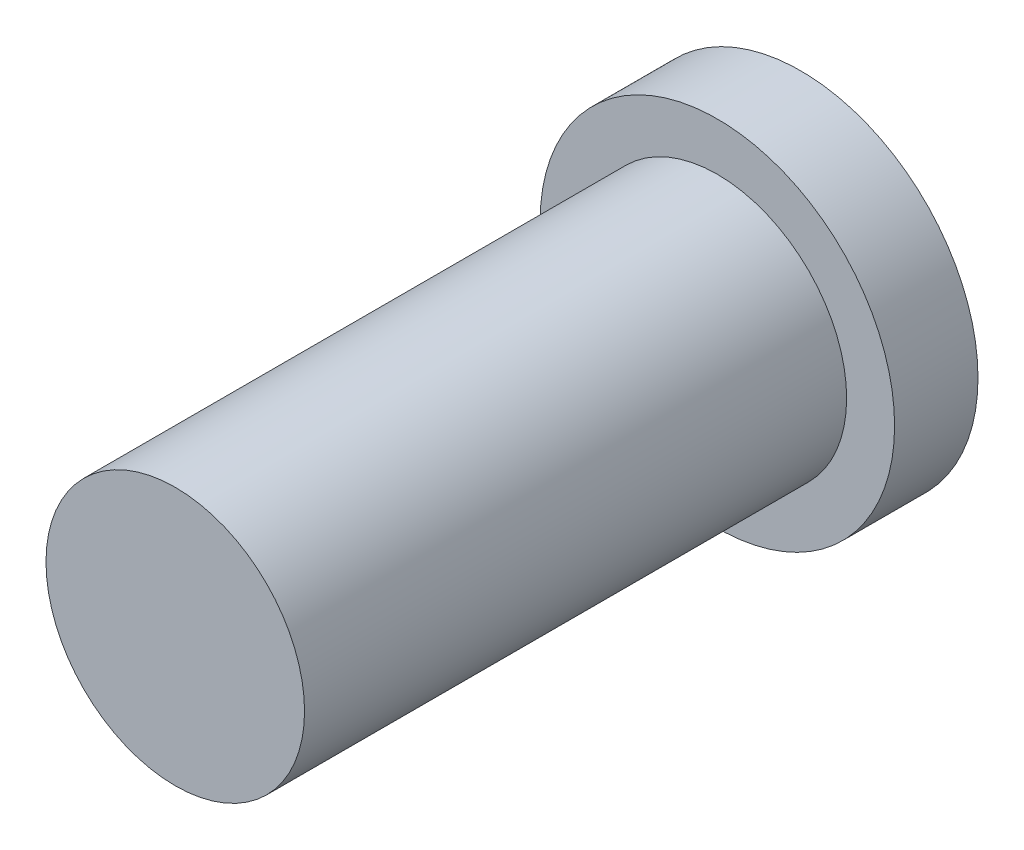
SolidWorks part; units mm, degrees
ref_plane "Front Plane" through (0, 0, 0) normal (0, 0, 1) x (1, 0, 0)
ref_plane "Top Plane" through (0, 0, 0) normal (0, 1, 0) x (1, 0, 0)
ref_plane "Right Plane" through (0, 0, 0) normal (1, 0, 0) x (0, 0, -1)
sketch "Sketch2" plane through (0, 0, 0) normal (0, 0, 1) x (1, 0, 0)
  circle A0 centre (0, 0) radius 5.3975
  dimension "D1" = 10.795
extrude "Boss-Extrude1" add sketch "Sketch2" along normal blind 2.54
sketch "Sketch3" plane through (0, 0, 2.54) normal (0, 0, 1) x (1, 0, 0)
  circle A0 centre (0, 0) radius 3.937
  dimension "D1" = 7.874
extrude "Boss-Extrude3" add sketch "Sketch3" along normal blind 16.51
